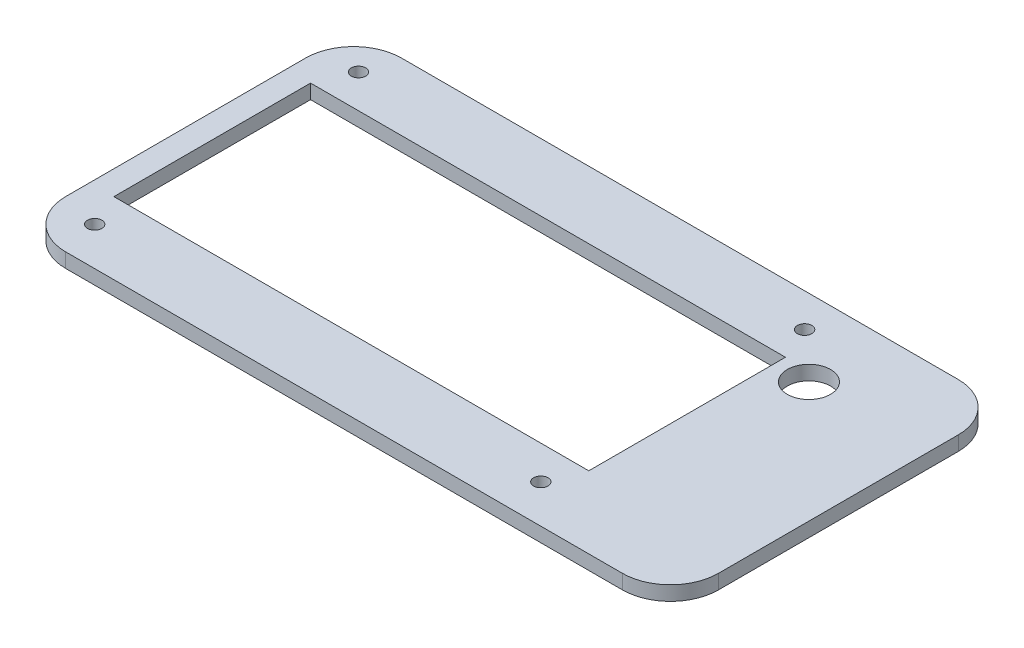
SolidWorks part; units mm, degrees
ref_plane "Front Plane" through (0, 0, 0) normal (0, 0, 1) x (1, 0, 0)
ref_plane "Top Plane" through (0, 0, 0) normal (0, 1, 0) x (1, 0, 0)
ref_plane "Right Plane" through (0, 0, 0) normal (1, 0, 0) x (0, 0, -1)
sketch "Sketch1" plane through (0, 0, 0) normal (0, 1, 0) x (1, 0, 0)
  line L0 (69.0949, -38.021) -> (69.0949, 11.979)
  line L1 (-56.9683, 21.979) -> (59.0949, 21.979)
  line L2 (-66.9683, 11.979) -> (-66.9683, -38.021)
  line L3 (-56.9683, -48.021) -> (59.0949, -48.021)
  line L4 (-61.9317, 7.979) -> (37.0683, 7.979)
  line L5 (-61.4317, 7.479) -> (36.5683, 7.479) construction
  line L6 (-61.4317, 7.479) -> (-61.4317, -32.521) construction
  line L7 (-61.4317, -32.521) -> (36.5683, -32.521) construction
  line L8 (36.5683, 7.479) -> (36.5683, -32.521) construction
  line L9 (37.0683, 7.979) -> (37.0683, -33.021)
  line L10 (-61.9317, -33.021) -> (37.0683, -33.021)
  line L11 (-61.9317, 7.979) -> (-61.9317, -33.021)
  circle A0 centre (-58.9317, 14.979) radius 1.5
  arc A1 (-66.9683, -38.021) -> (-56.9683, -48.021) centre (-56.9683, -38.021) ccw
  circle A2 centre (34.0683, 14.979) radius 1.5
  circle A3 centre (-58.9317, -40.021) radius 1.5
  circle A4 centre (34.0683, -40.021) radius 1.5
  circle A5 centre (43.9683, 5.979) radius 4.5
  circle A6 centre (-47.9317, 14.9831) radius 3.5 construction
  arc A7 (-56.9683, 21.979) -> (-66.9683, 11.979) centre (-56.9683, 11.979) ccw
  arc A8 (59.0949, 21.979) -> (69.0949, 11.979) centre (59.0949, 11.979) cw
  arc A9 (59.0949, -48.021) -> (69.0949, -38.021) centre (59.0949, -38.021) ccw
  point P22 (-66.9683, -48.021)
  point P25 (-66.9683, 21.979)
  dimension "D14" = 7
  dimension "D16" = 9
  dimension "D18" = 7
  dimension "D3" = 10
  dimension "D4" = 0.5
  dimension "D19" = 9
  dimension "D20" = 9.9
extrude "Boss-Extrude1" add sketch "Sketch1" along normal blind 3
